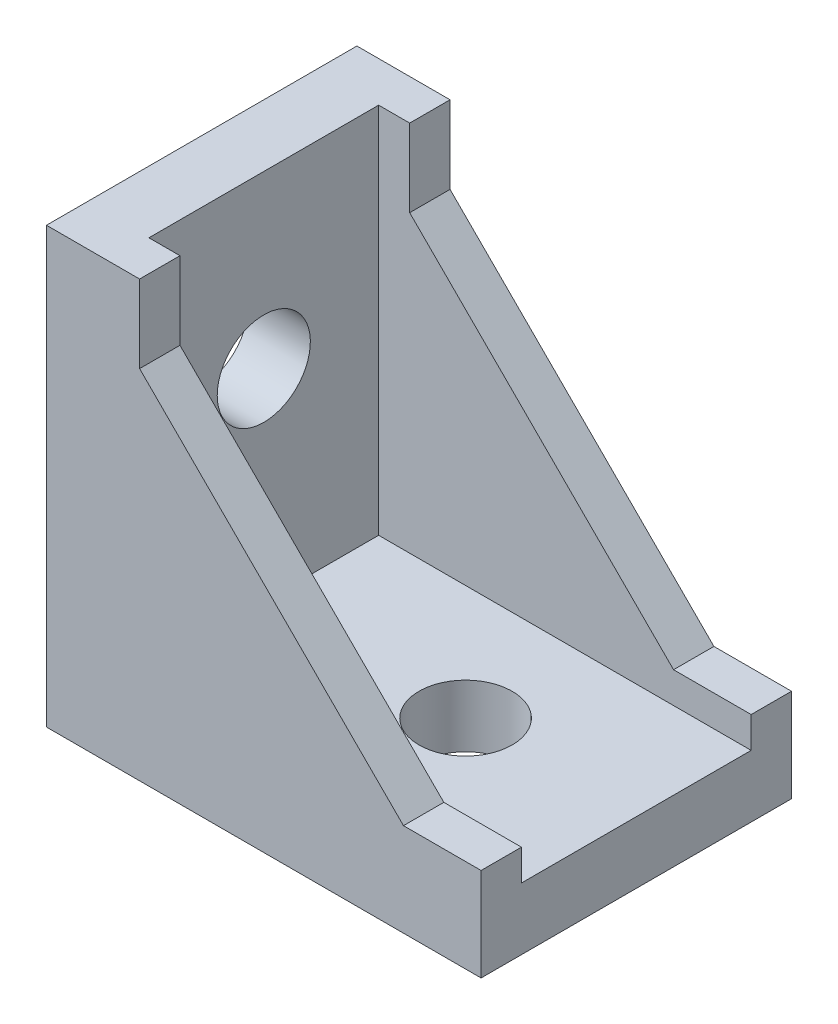
SolidWorks part; units mm, degrees
ref_plane "前视基准面" through (0, 0, 0) normal (0, 0, 1) x (1, 0, 0)
ref_plane "上视基准面" through (0, 0, 0) normal (0, 1, 0) x (1, 0, 0)
ref_plane "右视基准面" through (0, 0, 0) normal (1, 0, 0) x (0, 0, -1)
sketch "草图1" plane through (0, 0, 0) normal (0, 0, 1) x (1, 0, 0)
  line L0 (0, 0) -> (0, 28)
  line L1 (-0.089, -0.089) -> (31.3329, 31.3329) construction
  line L2 (0, 28) -> (4, 28)
  line L3 (4, 28) -> (4, 4)
  line L4 (28, 4) -> (4, 4)
  line L5 (28, 0) -> (28, 4)
  line L6 (0, 0) -> (28, 0)
  dimension "D1" = 28
  dimension "D2" = 4
extrude "凸台-拉伸1" add sketch "草图1" along normal blind 20
sketch "草图2" plane through (0, 0, 20) normal (0, 0, 1) x (1, 0, 0)
  line L0 (4, 28) -> (6, 28)
  line L1 (6, 28) -> (6, 23)
  line L2 (28, 4) -> (28, 6)
  line L3 (28, 6) -> (23, 6)
  line L4 (6, 23) -> (23, 6)
  line L5 (4, 28) -> (4, 4)
  line L6 (4, 4) -> (28, 4)
  dimension "D1" = 2
  dimension "D2" = 5
  dimension "D3" = 2
  dimension "D4" = 5
extrude "凸台-拉伸2" add sketch "草图2" against normal blind 2.6
ref_plane "基准面1" through (0, 0, 10) normal (0, 0, -1) x (-1, 0, 0)
mirror "镜向1" about plane through (0, 0, 10) normal (0, 0, -1) of "凸台-拉伸2"
sketch "草图3" plane through (0, 0, 0) normal (-1, 0, 0) x (0, 0, 1)
  line L0 (10, 28) -> (10, 0) construction
  line L1 (20, 28) -> (0, 28) construction
  line L2 (20, 0) -> (0, 0) construction
  line L3 (13, 26) -> (13, 24)
  line L4 (13, 26) -> (7, 26)
  line L5 (0, 14) -> (20, 14) construction
  line L6 (13, 24) -> (7, 24)
  line L7 (7, 26) -> (7, 24)
  line L8 (0, 28) -> (0, 0) construction
  line L9 (20, 28) -> (20, 0) construction
  line L10 (7, 2) -> (7, 4)
  line L11 (13, 4) -> (7, 4)
  line L12 (13, 2) -> (7, 2)
  line L13 (13, 2) -> (13, 4)
  point P8 (10, 26)
  point P14 (10, 24)
  point P22 (10, 4)
  point P23 (10, 2)
  dimension "D1" = 2
  dimension "D2" = 2
  dimension "D3" = 3
extrude "凸台-拉伸3" add sketch "草图3" along normal blind 1.5
ref_plane "基准面2" through (0, 0, 0) normal (-0.7071, 0.7071, 0) x (0, 0, 1)
mirror "镜向2" about plane through (0, 0, 0) normal (-0.7071, 0.7071, 0) of "凸台-拉伸3"
sketch "草图4" plane through (0, 0, 0) normal (-1, 0, 0) x (0, 0, 1)
  line L0 (10, 28) -> (10, 0) construction
  line L1 (20, 28) -> (0, 28) construction
  line L2 (20, 0) -> (0, 0) construction
  circle A0 centre (10, 17) radius 3
  dimension "D1" = 6
  dimension "D2" = 11
extrude "切除-拉伸1" cut sketch "草图4" against normal up to next (4 mm away)
mirror "镜向3" about plane through (0, 0, 0) normal (-0.7071, 0.7071, 0) of "切除-拉伸1"
